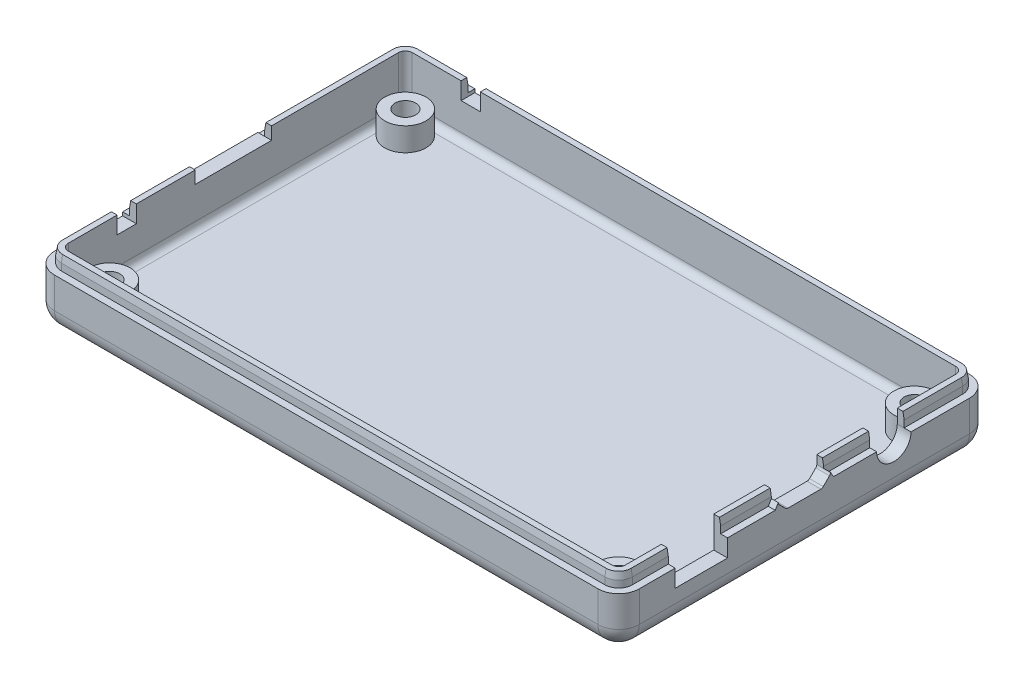
SolidWorks part; units mm, degrees
ref_plane "前视基准面" through (0, 0, 0) normal (0, 0, 1) x (1, 0, 0)
ref_plane "上视基准面" through (0, 0, 0) normal (0, 1, 0) x (1, 0, 0)
ref_plane "右视基准面" through (0, 0, 0) normal (1, 0, 0) x (0, 0, -1)
sketch "草图1" plane through (0, 0, 0) normal (0, 1, 0) x (1, 0, 0)
  line L1 (-42.5, 27) -> (42.5, 27)
  line L2 (-42.5, 27) -> (-42.5, -27)
  line L3 (-42.5, -27) -> (42.5, -27)
  line L4 (42.5, 27) -> (42.5, -27)
  line L5 (-42.5, 27) -> (42.5, -27) construction
  line L6 (-42.5, -27) -> (42.5, 27) construction
  point P0 (0, 0)
  dimension "D1" = 85
  dimension "D2" = 54
extrude "整体外形" add sketch "草图1" along normal blind 7.5
fillet "外形圆角" radius 3 8 edges at (0, 0, -27) (-42.5, 0, 0) (0, 0, 27) (42.5, 0, 0) (42.5, 3.75, 27) (-42.5, 3.75, 27) (-42.5, 3.75, -27) (42.5, 3.75, -27)
sketch "草图14" plane through (0, 7.5, 0) normal (0, 1, 0) x (1, 0, 0)
  line L8 (-39.5, -25) -> (39.5, -25)
  line L9 (40.5, -24) -> (40.5, 24)
  line L10 (39.5, 25) -> (-39.5, 25)
  line L11 (-40.5, 24) -> (-40.5, -24)
  line L12 (-39.5, -25) -> (39.5, -25)
  line L13 (40.5, -24) -> (40.5, 24)
  line L14 (39.5, 25) -> (-39.5, 25)
  line L15 (-40.5, 24) -> (-40.5, -24)
  arc A4 (39.5, -25) -> (40.5, -24) centre (39.5, -24) ccw
  arc A5 (39.5, -25) -> (40.5, -24) centre (39.5, -24) ccw
  arc A6 (40.5, 24) -> (39.5, 25) centre (39.5, 24) ccw
  arc A7 (40.5, 24) -> (39.5, 25) centre (39.5, 24) ccw
  arc A8 (-39.5, 25) -> (-40.5, 24) centre (-39.5, 24) ccw
  arc A9 (-39.5, 25) -> (-40.5, 24) centre (-39.5, 24) ccw
  arc A10 (-40.5, -24) -> (-39.5, -25) centre (-39.5, -24) ccw
  arc A11 (-40.5, -24) -> (-39.5, -25) centre (-39.5, -24) ccw
  dimension "D1" = 2
extrude "内腔" cut sketch "草图14" against normal offset from surface (5.5 mm away) 2 up to face at (0, 0, 0)
fillet "内腔圆角" radius 1 8 edges at (0, 2, 25) (-40.2071, 2, 24.7071) (-40.5, 2, 0) (-40.2071, 2, -24.7071) (0, 2, -25) (40.2071, 2, -24.7071) (40.5, 2, 0) (40.2071, 2, 24.7071)
sketch "草图15" plane through (0, 7.5, 0) normal (0, 1, 0) x (1, 0, 0)
  line L20 (-39.5, -26) -> (39.5, -26)
  line L21 (41.5, -24) -> (41.5, 24)
  line L22 (39.5, 26) -> (-39.5, 26)
  line L23 (-39.5, -25) -> (39.5, -25)
  line L24 (40.5, -24) -> (40.5, 24)
  line L25 (39.5, 25) -> (-39.5, 25)
  line L26 (-40.5, 24) -> (-40.5, -24)
  line L27 (-39.5, -25) -> (39.5, -25)
  line L28 (40.5, -24) -> (40.5, 24)
  line L29 (39.5, 25) -> (-39.5, 25)
  line L30 (-40.5, 24) -> (-40.5, -24)
  line L31 (-41.5, 24) -> (-41.5, -24)
  arc A20 (39.5, -26) -> (41.5, -24) centre (39.5, -24) ccw
  arc A21 (41.5, 24) -> (39.5, 26) centre (39.5, 24) ccw
  arc A22 (-39.5, 26) -> (-41.5, 24) centre (-39.5, 24) ccw
  arc A23 (-41.5, -24) -> (-39.5, -26) centre (-39.5, -24) ccw
  arc A24 (39.5, -25) -> (40.5, -24) centre (39.5, -24) ccw
  arc A25 (39.5, -25) -> (40.5, -24) centre (39.5, -24) ccw
  arc A26 (40.5, 24) -> (39.5, 25) centre (39.5, 24) ccw
  arc A27 (40.5, 24) -> (39.5, 25) centre (39.5, 24) ccw
  arc A28 (-39.5, 25) -> (-40.5, 24) centre (-39.5, 24) ccw
  arc A29 (-39.5, 25) -> (-40.5, 24) centre (-39.5, 24) ccw
  arc A30 (-40.5, -24) -> (-39.5, -25) centre (-39.5, -24) ccw
  arc A31 (-40.5, -24) -> (-39.5, -25) centre (-39.5, -24) ccw
  dimension "D1" = 2
  dimension "D2" = 1
extrude "咬合（凸）" add sketch "草图15" along normal blind 2
chamfer "咬合（凸）倒角" distance 1 angle 10 8 edges at (41.5, 9.5, 0) (40.9142, 9.5, -25.4142) (40.9142, 9.5, 25.4142) (0, 9.5, -26) (0, 9.5, 26) (-40.9142, 9.5, -25.4142) (-40.9142, 9.5, 25.4142) (-41.5, 9.5, 0)
extrude "耳机孔" cut sketch "草图16" against normal blind 5
sketch "草图16" plane through (42.5, 0, 0) normal (1, 0, 0) x (0, 0, -1)
  circle A0 centre (13, 7.5) radius 2.5
extrude "用户孔" cut sketch "草图19" against normal blind 10
sketch "草图19" plane through (42.5, 0, 0) normal (1, 0, 0) x (0, 0, -1)
  line L1 (-18.7884, 10.04) -> (-11.1684, 10.04)
  line L2 (-18.7884, 10.04) -> (-18.7884, 4.96)
  line L3 (-18.7884, 4.96) -> (-11.1684, 4.96)
  line L4 (-11.1684, 10.04) -> (-11.1684, 4.96)
  line L5 (-18.7884, 10.04) -> (-11.1684, 4.96) construction
  line L6 (-18.7884, 4.96) -> (-11.1684, 10.04) construction
  point P0 (-14.9784, 7.5)
extrude "切除-拉伸2" cut sketch "草图21" against normal blind 10
sketch "草图21" plane through (-42.5, 0, 0) normal (-1, 0, 0) x (0, 0, 1)
  line L20 (-5.55, 8.775) -> (-5.55, 7.675)
  line L21 (-5.55, 7.675) -> (5.55, 7.675)
  line L22 (5.55, 7.675) -> (5.55, 8.775)
  line L23 (5.55, 8.775) -> (-5.55, 8.775)
extrude "切除-拉伸3" cut sketch "草图22" against normal blind 10
sketch "草图22" plane through (-42.5, 0, 0) normal (-1, 0, 0) x (0, 0, 1)
  line L8 (-24, 7.5) -> (-15.2111, 7.5) construction
  line L25 (16.9, 8.2) -> (14.1, 8.2)
  line L26 (14.1, 8.2) -> (14.1, 7)
  line L27 (14.1, 7) -> (16.9, 7)
  line L28 (16.9, 7) -> (16.9, 8.2)
extrude "切除-拉伸5" cut sketch "草图25" against normal blind 10
sketch "草图25" plane through (42.5, 0, 0) normal (1, 0, 0) x (0, 0, -1)
  line L16 (3.8, 8.2571) -> (3.8, 8.95)
  line L17 (3.3, 9.45) -> (-3.3, 9.45)
  line L18 (-3.8, 8.95) -> (-3.8, 8.2571)
  line L19 (-3.6536, 7.9036) -> (-2.7464, 6.9964)
  line L20 (-2.3929, 6.85) -> (2.3929, 6.85)
  line L21 (2.7464, 6.9964) -> (3.6536, 7.9036)
  arc A12 (3.6536, 7.9036) -> (3.8, 8.2571) centre (3.3, 8.2571) ccw
  arc A13 (3.8, 8.95) -> (3.3, 9.45) centre (3.3, 8.95) ccw
  arc A14 (-3.3, 9.45) -> (-3.8, 8.95) centre (-3.3, 8.95) ccw
  arc A15 (-3.8, 8.2571) -> (-3.6536, 7.9036) centre (-3.3, 8.2571) ccw
  arc A16 (-2.7464, 6.9964) -> (-2.3929, 6.85) centre (-2.3929, 7.35) ccw
  arc A17 (2.3929, 6.85) -> (2.7464, 6.9964) centre (2.3929, 7.35) ccw
sketch "草图30" plane through (-41.5, 0, 0) normal (-1, 0, 0) x (0, 0, 1)
  line L0 (-24, 9.5) -> (24, 9.5) construction
  line L1 (-5.55, 8.775) -> (5.55, 8.775)
  line L2 (-5.55, 8.775) -> (-5.55, 9.5)
  line L3 (-5.55, 9.5) -> (5.55, 9.5)
  line L4 (5.55, 8.775) -> (5.55, 9.5)
  line L5 (-5.55, 8.775) -> (5.55, 9.5) construction
  line L6 (-5.55, 9.5) -> (5.55, 8.775) construction
  line L14 (14.1, 8.2) -> (16.9, 8.2)
  line L15 (14.1, 8.2) -> (14.1, 9.5)
  line L16 (14.1, 9.5) -> (16.9, 9.5)
  line L17 (16.9, 8.2) -> (16.9, 9.5)
  line L18 (14.1, 8.2) -> (16.9, 9.5) construction
  line L19 (14.1, 9.5) -> (16.9, 8.2) construction
  point P4 (0, 9.1375)
  point P23 (15.5, 8.85)
extrude "切除-拉伸6" cut sketch "草图30" against normal up to surface (1 mm away) up to face at (-40.5, 7.6, 15.5)
sketch "草图28" plane through (41.5, 0, 0) normal (1, 0, 0) x (0, 0, -1)
  line L0 (3.6536, 7.9036) -> (3.25, 7.5) construction
  line L1 (-3.25, 7.5) -> (-3.6536, 7.9036) construction
  line L2 (3.6536, 7.9036) -> (3.25, 7.5)
  line L3 (-3.25, 7.5) -> (-3.6536, 7.9036)
  line L4 (-3.8, 8.2571) -> (-4.2371, 7.5)
  line L5 (-11.1684, 7.5) -> (-3.25, 7.5) construction
  line L6 (-4.2371, 7.5) -> (-3.25, 7.5)
  line L7 (3.8, 8.2571) -> (4.2371, 7.5)
  line L8 (3.25, 7.5) -> (10.5, 7.5) construction
  line L9 (4.2371, 7.5) -> (3.25, 7.5)
  arc A0 (3.6536, 7.9036) -> (3.8, 8.2571) centre (3.3, 8.2571) ccw construction
  arc A1 (-3.8, 8.2571) -> (-3.6536, 7.9036) centre (-3.3, 8.2571) ccw construction
  arc A2 (3.6536, 7.9036) -> (3.8, 8.2571) centre (3.3, 8.2571) ccw
  arc A3 (-3.8, 8.2571) -> (-3.6536, 7.9036) centre (-3.3, 8.2571) ccw
  dimension "D1" = 60
  dimension "D2" = 60
extrude "凸台-拉伸2" add sketch "草图28" along normal up to surface (1 mm away) up to face at (42.5, 6.3152, 2.1196)
sketch "草图29" plane through (-41.5, 0, 0) normal (-1, 0, 0) x (0, 0, 1)
  line L0 (-5.55, 7.675) -> (-5.651, 7.5)
  line L1 (16.9, 7.5) -> (24, 7.5) construction
  line L2 (-5.651, 7.5) -> (5.651, 7.5)
  line L3 (16.9, 7.5) -> (24, 7.5) construction
  line L4 (5.651, 7.5) -> (5.55, 7.675)
  line L5 (5.55, 7.675) -> (-5.55, 7.675)
  dimension "D1" = 60
  dimension "D2" = 60
extrude "凸台-拉伸3" add sketch "草图29" along normal up to surface (1 mm away) up to face at (-42.5, 6.25, 7.75)
sketch "草图31" plane through (41.5, 0, 0) normal (1, 0, 0) x (0, 0, -1)
  line L0 (-11.1684, 9.5) -> (11.5, 9.5) construction
  line L1 (-3.8, 8.95) -> (3.8, 8.95)
  line L2 (-3.8, 8.95) -> (-3.8, 9.5)
  line L3 (-3.8, 9.5) -> (3.8, 9.5)
  line L4 (3.8, 8.95) -> (3.8, 9.5)
  line L5 (-3.8, 8.95) -> (3.8, 9.5) construction
  line L6 (-3.8, 9.5) -> (3.8, 8.95) construction
  line L7 (14.5, 9.5) -> (24, 9.5) construction
  line L8 (10.5, 7.5) -> (15.5, 7.5)
  line L9 (10.5, 7.5) -> (10.5, 9.5)
  line L10 (10.5, 9.5) -> (15.5, 9.5)
  line L11 (15.5, 7.5) -> (15.5, 9.5)
  line L12 (10.5, 7.5) -> (15.5, 9.5) construction
  line L13 (10.5, 9.5) -> (15.5, 7.5) construction
  line L14 (3.8, 8.5) -> (3.8, 8.95) construction
  point P4 (0, 9.225)
  point P12 (13, 8.5)
  point P19 (3.8, 8.725)
extrude "切除-拉伸7" cut sketch "草图31" against normal up to surface (1 mm away)
extrude "切除-拉伸8" cut sketch "草图32" against normal blind 10
sketch "草图32" plane through (0, 0, -27) normal (0, 0, -1) x (-1, 0, 0)
  line L12 (32.4, 8.2) -> (29.6, 8.2)
  line L13 (29.6, 8.2) -> (29.6, 7)
  line L14 (29.6, 7) -> (32.4, 7)
  line L15 (32.4, 7) -> (32.4, 8.2)
sketch "草图33" plane through (0, 0, -27) normal (0, 0, -1) x (-1, 0, 0)
  line L0 (-39.5, 9.5) -> (39.5, 9.5) construction
  line L1 (29.6, 8.2) -> (32.4, 8.2)
  line L2 (29.6, 8.2) -> (29.6, 9.5)
  line L3 (29.6, 9.5) -> (32.4, 9.5)
  line L4 (32.4, 8.2) -> (32.4, 9.5)
  line L5 (29.6, 8.2) -> (32.4, 9.5) construction
  line L6 (29.6, 9.5) -> (32.4, 8.2) construction
  point P4 (31, 8.85)
extrude "切除-拉伸9" cut sketch "草图33" against normal up to surface (2 mm away) up to face at (-31, 7.6, -25)
sketch "草图34" plane through (0, 2, 0) normal (0, 1, 0) x (1, 0, 0)
  line L0 (-40.5, 24) -> (-40.5, 5.55) construction
  line L2 (-32.4, 25) -> (-39.5, 25) construction
  circle A0 centre (-37, 21.5) radius 1.5
  circle A1 centre (-37, 21.5) radius 3
  dimension "D1" = 3
  dimension "D2" = 6
  dimension "D3" = 3.5
  dimension "D4" = 3.5
extrude "凸台-拉伸4" add sketch "草图34" along normal blind 3.4
pattern_linear "阵列(线性)1" count 2 spacing 74 along (1, 0, 0) count 2 spacing 43 along (0, 0, 1) of "凸台-拉伸4"
